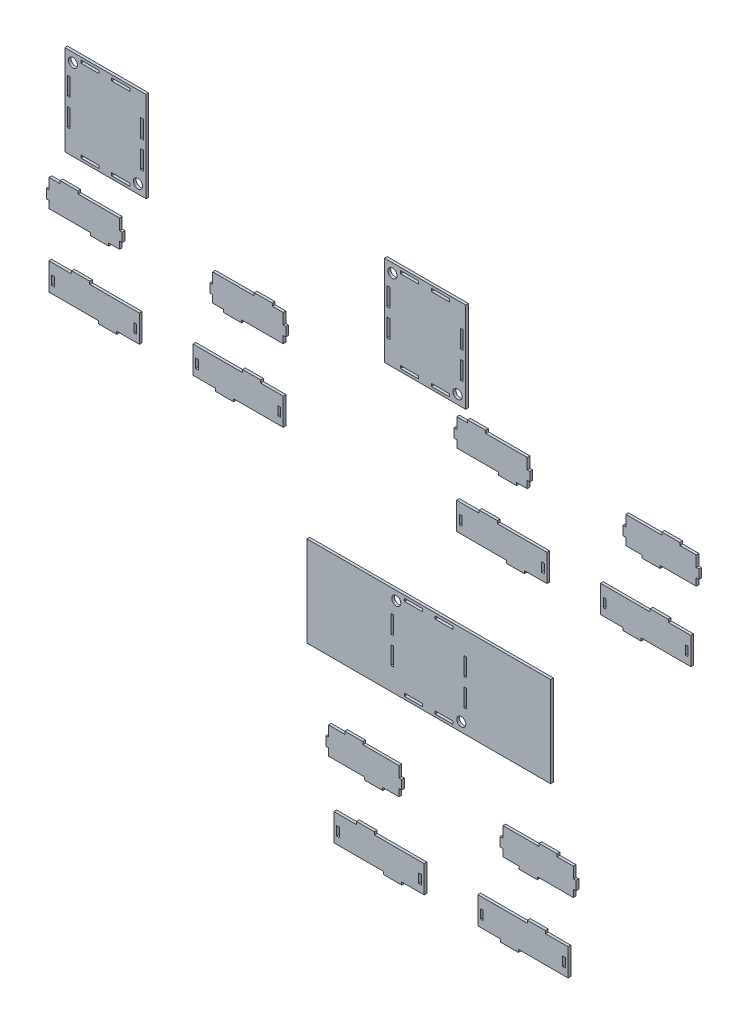
SolidWorks part; units mm, degrees
ref_plane "Спереди" through (0, 0, 0) normal (0, 0, 1) x (1, 0, 0)
ref_plane "Сверху" through (0, 0, 0) normal (0, 1, 0) x (1, 0, 0)
ref_plane "Справа" through (0, 0, 0) normal (1, 0, 0) x (0, 0, -1)
sketch "Эскиз1" plane through (0, 0, 0) normal (0, 0, 1) x (1, 0, 0)
  line L11 (-251.1655, 214.705) -> (-254.1655, 214.705)
  line L32 (-251.1655, 226.705) -> (-239.1655, 226.705)
  line L42 (-196.2718, 116.5938) -> (-196.2718, 113.5938)
  line L43 (-251.2718, 146.5938) -> (-226.2718, 146.5938)
  line L44 (-251.2718, 146.5938) -> (-251.2718, 116.5938)
  line L45 (-251.2718, 116.5938) -> (-196.2718, 116.5938)
  line L46 (-151.2718, 146.5938) -> (-151.2718, 116.5938)
  line L47 (-248.2718, 134.5938) -> (-245.2718, 134.5938)
  line L48 (-248.2718, 134.5938) -> (-248.2718, 124.5938)
  line L49 (-248.2718, 124.5938) -> (-245.2718, 124.5938)
  line L50 (-245.2718, 134.5938) -> (-245.2718, 124.5938)
  line L51 (-157.2718, 134.5938) -> (-154.2718, 134.5938)
  line L52 (-157.2718, 134.5938) -> (-157.2718, 124.5938)
  line L53 (-157.2718, 124.5938) -> (-154.2718, 124.5938)
  line L54 (-154.2718, 134.5938) -> (-154.2718, 124.5938)
  line L55 (-196.2718, 113.5938) -> (-176.2718, 113.5938)
  line L56 (-176.2718, 113.5938) -> (-176.2718, 116.5938)
  line L57 (-226.2718, 146.5938) -> (-226.2718, 149.5938)
  line L58 (-226.2718, 149.5938) -> (-206.2718, 149.5938)
  line L59 (-206.2718, 149.5938) -> (-206.2718, 146.5938)
  line L60 (-176.2718, 116.5938) -> (-151.2718, 116.5938)
  line L61 (-206.2718, 146.5938) -> (-151.2718, 146.5938)
  line L93 (-121.597, -804.4399) -> (-121.597, 49195.5601) construction
  line L114 (-58.0285, 196.705) -> (-70.0285, 196.705)
  line L175 (-70.0285, 204.705) -> (-70.0285, 196.705)
  line L196 (-24.0285, 226.705) -> (-70.0285, 226.705)
  line L247 (-233.8227, 359.8799) -> (-143.8227, 359.8799)
  line L248 (-233.8227, 359.8799) -> (-233.8227, 259.8799)
  line L249 (-233.8227, 259.8799) -> (-143.8227, 259.8799)
  line L250 (-143.8227, 359.8799) -> (-143.8227, 259.8799)
  line L251 (-230.8227, 304.8799) -> (-227.8227, 304.8799)
  line L252 (-230.8227, 304.8799) -> (-230.8227, 284.8799)
  line L253 (-230.8227, 284.8799) -> (-227.8227, 284.8799)
  line L254 (-227.8227, 304.8799) -> (-227.8227, 284.8799)
  line L255 (-215.8227, 356.8799) -> (-195.8227, 356.8799)
  line L256 (-215.8227, 356.8799) -> (-215.8227, 353.8799)
  line L257 (-215.8227, 353.8799) -> (-195.8227, 353.8799)
  line L258 (-195.8227, 356.8799) -> (-195.8227, 353.8799)
  line L259 (-146.8227, 304.8799) -> (-149.8227, 304.8799)
  line L260 (-146.8227, 304.8799) -> (-146.8227, 284.8799)
  line L261 (-146.8227, 284.8799) -> (-149.8227, 284.8799)
  line L262 (-149.8227, 304.8799) -> (-149.8227, 284.8799)
  line L263 (-215.8227, 262.8799) -> (-195.8227, 262.8799)
  line L264 (-215.8227, 262.8799) -> (-215.8227, 265.8799)
  line L265 (-215.8227, 265.8799) -> (-195.8227, 265.8799)
  line L266 (-195.8227, 262.8799) -> (-195.8227, 265.8799)
  line L267 (-181.8227, 353.8799) -> (-161.8227, 353.8799)
  line L268 (-181.8227, 353.8799) -> (-181.8227, 356.8799)
  line L269 (-181.8227, 356.8799) -> (-161.8227, 356.8799)
  line L270 (-161.8227, 353.8799) -> (-161.8227, 356.8799)
  line L271 (-146.8227, 334.8799) -> (-149.8227, 334.8799)
  line L272 (-146.8227, 334.8799) -> (-146.8227, 314.8799)
  line L273 (-146.8227, 314.8799) -> (-149.8227, 314.8799)
  line L274 (-149.8227, 334.8799) -> (-149.8227, 314.8799)
  line L275 (-230.8227, 334.8799) -> (-227.8227, 334.8799)
  line L276 (-230.8227, 334.8799) -> (-230.8227, 314.8799)
  line L277 (-230.8227, 314.8799) -> (-227.8227, 314.8799)
  line L278 (-227.8227, 334.8799) -> (-227.8227, 314.8799)
  line L279 (-181.8227, 265.8799) -> (-161.8227, 265.8799)
  line L280 (-181.8227, 265.8799) -> (-181.8227, 262.8799)
  line L281 (-181.8227, 262.8799) -> (-161.8227, 262.8799)
  line L282 (-161.8227, 265.8799) -> (-161.8227, 262.8799)
  line L318 (-251.1655, 226.705) -> (-251.1655, 214.705)
  line L319 (-251.1655, 196.705) -> (-205.1655, 196.705)
  line L320 (-173.1655, 226.705) -> (-173.1655, 214.705)
  line L321 (-254.1655, 214.705) -> (-254.1655, 204.705)
  line L322 (-254.1655, 204.705) -> (-251.1655, 204.705)
  line L323 (-205.1655, 196.705) -> (-205.1655, 193.705)
  line L324 (-205.1655, 193.705) -> (-185.1655, 193.705)
  line L325 (-185.1655, 193.705) -> (-185.1655, 196.705)
  line L326 (-173.1655, 214.705) -> (-170.1655, 214.705)
  line L327 (-170.1655, 214.705) -> (-170.1655, 204.705)
  line L328 (-170.1655, 204.705) -> (-173.1655, 204.705)
  line L329 (-239.1655, 226.705) -> (-239.1655, 229.705)
  line L330 (-239.1655, 229.705) -> (-219.1655, 229.705)
  line L331 (-219.1655, 229.705) -> (-219.1655, 226.705)
  line L332 (-251.1655, 204.705) -> (-251.1655, 196.705)
  line L333 (-219.1655, 226.705) -> (-173.1655, 226.705)
  line L334 (-173.1655, 204.705) -> (-173.1655, 196.705)
  line L335 (-185.1655, 196.705) -> (-173.1655, 196.705)
  line L336 (7.9715, 204.705) -> (7.9715, 196.705)
  line L337 (-24.0285, 229.705) -> (-24.0285, 226.705)
  line L338 (-4.0285, 229.705) -> (-24.0285, 229.705)
  line L339 (-4.0285, 226.705) -> (-4.0285, 229.705)
  line L340 (-73.0285, 204.705) -> (-70.0285, 204.705)
  line L341 (-73.0285, 214.705) -> (-73.0285, 204.705)
  line L342 (-70.0285, 214.705) -> (-73.0285, 214.705)
  line L343 (-58.0285, 193.705) -> (-58.0285, 196.705)
  line L344 (-38.0285, 193.705) -> (-58.0285, 193.705)
  line L345 (-38.0285, 196.705) -> (-38.0285, 193.705)
  line L346 (10.9715, 204.705) -> (7.9715, 204.705)
  line L347 (10.9715, 214.705) -> (10.9715, 204.705)
  line L348 (-70.0285, 226.705) -> (-70.0285, 214.705)
  line L349 (7.9715, 196.705) -> (-38.0285, 196.705)
  line L350 (7.9715, 226.705) -> (7.9715, 214.705)
  line L351 (-36.9222, 146.5938) -> (-91.9222, 146.5938)
  line L352 (-66.9222, 116.5938) -> (-91.9222, 116.5938)
  line L353 (-36.9222, 149.5938) -> (-36.9222, 146.5938)
  line L354 (-16.9222, 149.5938) -> (-36.9222, 149.5938)
  line L355 (-16.9222, 146.5938) -> (-16.9222, 149.5938)
  line L356 (-66.9222, 113.5938) -> (-66.9222, 116.5938)
  line L357 (-46.9222, 113.5938) -> (-66.9222, 113.5938)
  line L358 (-88.9222, 134.5938) -> (-88.9222, 124.5938)
  line L359 (-85.9222, 124.5938) -> (-88.9222, 124.5938)
  line L360 (-85.9222, 134.5938) -> (-85.9222, 124.5938)
  line L361 (-85.9222, 134.5938) -> (-88.9222, 134.5938)
  line L362 (2.0778, 134.5938) -> (2.0778, 124.5938)
  line L363 (5.0778, 124.5938) -> (2.0778, 124.5938)
  line L364 (5.0778, 134.5938) -> (5.0778, 124.5938)
  line L365 (5.0778, 134.5938) -> (2.0778, 134.5938)
  line L366 (-91.9222, 146.5938) -> (-91.9222, 116.5938)
  line L367 (8.0778, 116.5938) -> (-46.9222, 116.5938)
  line L368 (8.0778, 146.5938) -> (8.0778, 116.5938)
  line L369 (8.0778, 146.5938) -> (-16.9222, 146.5938)
  line L370 (-46.9222, 116.5938) -> (-46.9222, 113.5938)
  line L371 (7.9715, 226.705) -> (-4.0285, 226.705)
  line L372 (7.9715, 214.705) -> (10.9715, 214.705)
  line L398 (120.1372, 334.937) -> (210.1372, 334.937)
  line L399 (120.1372, 334.937) -> (120.1372, 234.937)
  line L400 (120.1372, 234.937) -> (210.1372, 234.937)
  line L401 (210.1372, 334.937) -> (210.1372, 234.937)
  line L402 (123.1372, 279.937) -> (126.1372, 279.937)
  line L403 (123.1372, 279.937) -> (123.1372, 259.937)
  line L404 (123.1372, 259.937) -> (126.1372, 259.937)
  line L405 (126.1372, 279.937) -> (126.1372, 259.937)
  line L406 (138.1372, 331.937) -> (158.1372, 331.937)
  line L407 (138.1372, 331.937) -> (138.1372, 328.937)
  line L408 (138.1372, 328.937) -> (158.1372, 328.937)
  line L409 (158.1372, 331.937) -> (158.1372, 328.937)
  line L410 (207.1372, 279.937) -> (204.1372, 279.937)
  line L411 (207.1372, 279.937) -> (207.1372, 259.937)
  line L412 (207.1372, 259.937) -> (204.1372, 259.937)
  line L413 (204.1372, 279.937) -> (204.1372, 259.937)
  line L414 (138.1372, 237.937) -> (158.1372, 237.937)
  line L415 (138.1372, 237.937) -> (138.1372, 240.937)
  line L416 (138.1372, 240.937) -> (158.1372, 240.937)
  line L417 (158.1372, 237.937) -> (158.1372, 240.937)
  line L418 (172.1372, 328.937) -> (192.1372, 328.937)
  line L419 (172.1372, 328.937) -> (172.1372, 331.937)
  line L420 (172.1372, 331.937) -> (192.1372, 331.937)
  line L421 (192.1372, 328.937) -> (192.1372, 331.937)
  line L422 (207.1372, 309.937) -> (204.1372, 309.937)
  line L423 (207.1372, 309.937) -> (207.1372, 289.937)
  line L424 (207.1372, 289.937) -> (204.1372, 289.937)
  line L425 (204.1372, 309.937) -> (204.1372, 289.937)
  line L426 (123.1372, 309.937) -> (126.1372, 309.937)
  line L427 (123.1372, 309.937) -> (123.1372, 289.937)
  line L428 (123.1372, 289.937) -> (126.1372, 289.937)
  line L429 (126.1372, 309.937) -> (126.1372, 289.937)
  line L430 (172.1372, 240.937) -> (192.1372, 240.937)
  line L431 (172.1372, 240.937) -> (172.1372, 237.937)
  line L432 (172.1372, 237.937) -> (192.1372, 237.937)
  line L433 (192.1372, 240.937) -> (192.1372, 237.937)
  line L514 (124.2667, 22.8612) -> (214.2667, 22.8612)
  line L516 (124.2667, -77.1388) -> (214.2667, -77.1388)
  line L518 (127.2667, -32.1388) -> (130.2667, -32.1388)
  line L519 (127.2667, -32.1388) -> (127.2667, -52.1388)
  line L520 (127.2667, -52.1388) -> (130.2667, -52.1388)
  line L521 (130.2667, -32.1388) -> (130.2667, -52.1388)
  line L522 (142.2667, 19.8612) -> (162.2667, 19.8612)
  line L523 (142.2667, 19.8612) -> (142.2667, 16.8612)
  line L524 (142.2667, 16.8612) -> (162.2667, 16.8612)
  line L525 (162.2667, 19.8612) -> (162.2667, 16.8612)
  line L526 (211.2667, -32.1388) -> (208.2667, -32.1388)
  line L527 (211.2667, -32.1388) -> (211.2667, -52.1388)
  line L528 (211.2667, -52.1388) -> (208.2667, -52.1388)
  line L529 (208.2667, -32.1388) -> (208.2667, -52.1388)
  line L530 (142.2667, -74.1388) -> (162.2667, -74.1388)
  line L531 (142.2667, -74.1388) -> (142.2667, -71.1388)
  line L532 (142.2667, -71.1388) -> (162.2667, -71.1388)
  line L533 (162.2667, -74.1388) -> (162.2667, -71.1388)
  line L534 (176.2667, 16.8612) -> (196.2667, 16.8612)
  line L535 (176.2667, 16.8612) -> (176.2667, 19.8612)
  line L536 (176.2667, 19.8612) -> (196.2667, 19.8612)
  line L537 (196.2667, 16.8612) -> (196.2667, 19.8612)
  line L538 (211.2667, -2.1388) -> (208.2667, -2.1388)
  line L539 (211.2667, -2.1388) -> (211.2667, -22.1388)
  line L540 (211.2667, -22.1388) -> (208.2667, -22.1388)
  line L541 (208.2667, -2.1388) -> (208.2667, -22.1388)
  line L542 (127.2667, -2.1388) -> (130.2667, -2.1388)
  line L543 (127.2667, -2.1388) -> (127.2667, -22.1388)
  line L544 (127.2667, -22.1388) -> (130.2667, -22.1388)
  line L545 (130.2667, -2.1388) -> (130.2667, -22.1388)
  line L546 (176.2667, -71.1388) -> (196.2667, -71.1388)
  line L547 (176.2667, -71.1388) -> (176.2667, -74.1388)
  line L548 (176.2667, -74.1388) -> (196.2667, -74.1388)
  line L549 (196.2667, -71.1388) -> (196.2667, -74.1388)
  line L605 (124.2667, 22.8612) -> (34.2667, 22.8612)
  line L610 (34.2667, 22.8612) -> (34.2667, -77.1388)
  line L611 (34.2667, -77.1388) -> (124.2667, -77.1388)
  line L612 (214.2667, -77.1388) -> (304.2667, -77.1388)
  line L613 (304.2667, -77.1388) -> (304.2667, 22.8612)
  line L614 (304.2667, 22.8612) -> (214.2667, 22.8612)
  line L615 (200.25, 210.8868) -> (197.25, 210.8868)
  line L616 (200.25, 222.8868) -> (212.25, 222.8868)
  line L617 (255.1437, 112.7755) -> (255.1437, 109.7755)
  line L618 (200.1437, 142.7755) -> (225.1437, 142.7755)
  line L619 (200.1437, 142.7755) -> (200.1437, 112.7755)
  line L620 (200.1437, 112.7755) -> (255.1437, 112.7755)
  line L621 (300.1437, 142.7755) -> (300.1437, 112.7755)
  line L622 (203.1437, 130.7755) -> (206.1437, 130.7755)
  line L623 (203.1437, 130.7755) -> (203.1437, 120.7755)
  line L624 (203.1437, 120.7755) -> (206.1437, 120.7755)
  line L625 (206.1437, 130.7755) -> (206.1437, 120.7755)
  line L626 (294.1437, 130.7755) -> (297.1437, 130.7755)
  line L627 (294.1437, 130.7755) -> (294.1437, 120.7755)
  line L628 (294.1437, 120.7755) -> (297.1437, 120.7755)
  line L629 (297.1437, 130.7755) -> (297.1437, 120.7755)
  line L630 (255.1437, 109.7755) -> (275.1437, 109.7755)
  line L631 (275.1437, 109.7755) -> (275.1437, 112.7755)
  line L632 (225.1437, 142.7755) -> (225.1437, 145.7755)
  line L633 (225.1437, 145.7755) -> (245.1437, 145.7755)
  line L634 (245.1437, 145.7755) -> (245.1437, 142.7755)
  line L635 (275.1437, 112.7755) -> (300.1437, 112.7755)
  line L636 (245.1437, 142.7755) -> (300.1437, 142.7755)
  line L637 (405.387, 192.8868) -> (387.387, 192.8868)
  line L638 (387.387, 200.8868) -> (387.387, 192.8868)
  line L639 (427.387, 222.8868) -> (387.387, 222.8868)
  line L640 (200.25, 222.8868) -> (200.25, 210.8868)
  line L641 (200.25, 192.8868) -> (246.25, 192.8868)
  line L642 (278.25, 222.8868) -> (278.25, 210.8868)
  line L643 (197.25, 210.8868) -> (197.25, 200.8868)
  line L644 (197.25, 200.8868) -> (200.25, 200.8868)
  line L645 (246.25, 192.8868) -> (246.25, 189.8868)
  line L646 (246.25, 189.8868) -> (266.25, 189.8868)
  line L647 (266.25, 189.8868) -> (266.25, 192.8868)
  line L648 (278.25, 210.8868) -> (281.25, 210.8868)
  line L649 (281.25, 210.8868) -> (281.25, 200.8868)
  line L650 (281.25, 200.8868) -> (278.25, 200.8868)
  line L651 (212.25, 222.8868) -> (212.25, 225.8868)
  line L652 (212.25, 225.8868) -> (232.25, 225.8868)
  line L653 (232.25, 225.8868) -> (232.25, 222.8868)
  line L654 (200.25, 200.8868) -> (200.25, 192.8868)
  line L655 (232.25, 222.8868) -> (278.25, 222.8868)
  line L656 (278.25, 200.8868) -> (278.25, 192.8868)
  line L657 (266.25, 192.8868) -> (278.25, 192.8868)
  line L658 (465.387, 200.8868) -> (465.387, 192.8868)
  line L659 (427.387, 225.8868) -> (427.387, 222.8868)
  line L660 (447.387, 225.8868) -> (427.387, 225.8868)
  line L661 (447.387, 222.8868) -> (447.387, 225.8868)
  line L662 (384.387, 200.8868) -> (387.387, 200.8868)
  line L663 (384.387, 210.8868) -> (384.387, 200.8868)
  line L664 (387.387, 210.8868) -> (384.387, 210.8868)
  line L665 (405.387, 189.8868) -> (405.387, 192.8868)
  line L666 (425.387, 189.8868) -> (405.387, 189.8868)
  line L667 (425.387, 192.8868) -> (425.387, 189.8868)
  line L668 (468.387, 200.8868) -> (465.387, 200.8868)
  line L669 (468.387, 210.8868) -> (468.387, 200.8868)
  line L670 (387.387, 222.8868) -> (387.387, 210.8868)
  line L671 (465.387, 192.8868) -> (425.387, 192.8868)
  line L672 (465.387, 222.8868) -> (465.387, 210.8868)
  line L673 (414.4934, 142.7755) -> (359.4934, 142.7755)
  line L674 (384.4934, 112.7755) -> (359.4934, 112.7755)
  line L675 (414.4934, 145.7755) -> (414.4934, 142.7755)
  line L676 (434.4934, 145.7755) -> (414.4934, 145.7755)
  line L677 (434.4934, 142.7755) -> (434.4934, 145.7755)
  line L678 (384.4934, 109.7755) -> (384.4934, 112.7755)
  line L679 (404.4934, 109.7755) -> (384.4934, 109.7755)
  line L680 (362.4934, 130.7755) -> (362.4934, 120.7755)
  line L681 (365.4934, 120.7755) -> (362.4934, 120.7755)
  line L682 (365.4934, 130.7755) -> (365.4934, 120.7755)
  line L683 (365.4934, 130.7755) -> (362.4934, 130.7755)
  line L684 (453.4934, 130.7755) -> (453.4934, 120.7755)
  line L685 (456.4934, 120.7755) -> (453.4934, 120.7755)
  line L686 (456.4934, 130.7755) -> (456.4934, 120.7755)
  line L687 (456.4934, 130.7755) -> (453.4934, 130.7755)
  line L688 (359.4934, 142.7755) -> (359.4934, 112.7755)
  line L689 (459.4934, 112.7755) -> (404.4934, 112.7755)
  line L690 (459.4934, 142.7755) -> (459.4934, 112.7755)
  line L691 (459.4934, 142.7755) -> (434.4934, 142.7755)
  line L692 (404.4934, 112.7755) -> (404.4934, 109.7755)
  line L693 (465.387, 222.8868) -> (447.387, 222.8868)
  line L694 (465.387, 210.8868) -> (468.387, 210.8868)
  line L695 (58.2619, -155.6255) -> (55.2619, -155.6255)
  line L696 (58.2619, -143.6255) -> (76.2619, -143.6255)
  line L697 (119.1556, -253.7368) -> (119.1556, -256.7368)
  line L698 (64.1556, -223.7368) -> (89.1556, -223.7368)
  line L699 (64.1556, -223.7368) -> (64.1556, -253.7368)
  line L700 (64.1556, -253.7368) -> (119.1556, -253.7368)
  line L701 (164.1556, -223.7368) -> (164.1556, -253.7368)
  line L702 (67.1556, -235.7368) -> (70.1556, -235.7368)
  line L703 (67.1556, -235.7368) -> (67.1556, -245.7368)
  line L704 (67.1556, -245.7368) -> (70.1556, -245.7368)
  line L705 (70.1556, -235.7368) -> (70.1556, -245.7368)
  line L706 (158.1556, -235.7368) -> (161.1556, -235.7368)
  line L707 (158.1556, -235.7368) -> (158.1556, -245.7368)
  line L708 (158.1556, -245.7368) -> (161.1556, -245.7368)
  line L709 (161.1556, -235.7368) -> (161.1556, -245.7368)
  line L710 (119.1556, -256.7368) -> (139.1556, -256.7368)
  line L711 (139.1556, -256.7368) -> (139.1556, -253.7368)
  line L712 (89.1556, -223.7368) -> (89.1556, -220.7368)
  line L713 (89.1556, -220.7368) -> (109.1556, -220.7368)
  line L714 (109.1556, -220.7368) -> (109.1556, -223.7368)
  line L715 (139.1556, -253.7368) -> (164.1556, -253.7368)
  line L716 (109.1556, -223.7368) -> (164.1556, -223.7368)
  line L717 (269.3989, -173.6255) -> (251.3989, -173.6255)
  line L718 (251.3989, -165.6255) -> (251.3989, -173.6255)
  line L719 (291.3989, -143.6255) -> (251.3989, -143.6255)
  line L720 (58.2619, -143.6255) -> (58.2619, -155.6255)
  line L721 (58.2619, -173.6255) -> (98.2619, -173.6255)
  line L722 (136.2619, -143.6255) -> (136.2619, -155.6255)
  line L723 (55.2619, -155.6255) -> (55.2619, -165.6255)
  line L724 (55.2619, -165.6255) -> (58.2619, -165.6255)
  line L725 (98.2619, -173.6255) -> (98.2619, -176.6255)
  line L726 (98.2619, -176.6255) -> (118.2619, -176.6255)
  line L727 (118.2619, -176.6255) -> (118.2619, -173.6255)
  line L728 (136.2619, -155.6255) -> (139.2619, -155.6255)
  line L729 (139.2619, -155.6255) -> (139.2619, -165.6255)
  line L730 (139.2619, -165.6255) -> (136.2619, -165.6255)
  line L731 (76.2619, -143.6255) -> (76.2619, -140.6255)
  line L732 (76.2619, -140.6255) -> (96.2619, -140.6255)
  line L733 (96.2619, -140.6255) -> (96.2619, -143.6255)
  line L734 (58.2619, -165.6255) -> (58.2619, -173.6255)
  line L735 (96.2619, -143.6255) -> (136.2619, -143.6255)
  line L736 (136.2619, -165.6255) -> (136.2619, -173.6255)
  line L737 (118.2619, -173.6255) -> (136.2619, -173.6255)
  line L738 (329.3989, -165.6255) -> (329.3989, -173.6255)
  line L739 (291.3989, -140.6255) -> (291.3989, -143.6255)
  line L740 (311.3989, -140.6255) -> (291.3989, -140.6255)
  line L741 (311.3989, -143.6255) -> (311.3989, -140.6255)
  line L742 (248.3989, -165.6255) -> (251.3989, -165.6255)
  line L743 (248.3989, -155.6255) -> (248.3989, -165.6255)
  line L744 (251.3989, -155.6255) -> (248.3989, -155.6255)
  line L745 (269.3989, -176.6255) -> (269.3989, -173.6255)
  line L746 (289.3989, -176.6255) -> (269.3989, -176.6255)
  line L747 (289.3989, -173.6255) -> (289.3989, -176.6255)
  line L748 (332.3989, -165.6255) -> (329.3989, -165.6255)
  line L749 (332.3989, -155.6255) -> (332.3989, -165.6255)
  line L750 (251.3989, -143.6255) -> (251.3989, -155.6255)
  line L751 (329.3989, -173.6255) -> (289.3989, -173.6255)
  line L752 (329.3989, -143.6255) -> (329.3989, -155.6255)
  line L753 (278.5052, -223.7368) -> (223.5052, -223.7368)
  line L754 (248.5052, -253.7368) -> (223.5052, -253.7368)
  line L755 (278.5052, -220.7368) -> (278.5052, -223.7368)
  line L756 (298.5052, -220.7368) -> (278.5052, -220.7368)
  line L757 (298.5052, -223.7368) -> (298.5052, -220.7368)
  line L758 (248.5052, -256.7368) -> (248.5052, -253.7368)
  line L759 (268.5052, -256.7368) -> (248.5052, -256.7368)
  line L760 (226.5052, -235.7368) -> (226.5052, -245.7368)
  line L761 (229.5052, -245.7368) -> (226.5052, -245.7368)
  line L762 (229.5052, -235.7368) -> (229.5052, -245.7368)
  line L763 (229.5052, -235.7368) -> (226.5052, -235.7368)
  line L764 (317.5052, -235.7368) -> (317.5052, -245.7368)
  line L765 (320.5052, -245.7368) -> (317.5052, -245.7368)
  line L766 (320.5052, -235.7368) -> (320.5052, -245.7368)
  line L767 (320.5052, -235.7368) -> (317.5052, -235.7368)
  line L768 (223.5052, -223.7368) -> (223.5052, -253.7368)
  line L769 (323.5052, -253.7368) -> (268.5052, -253.7368)
  line L770 (323.5052, -223.7368) -> (323.5052, -253.7368)
  line L771 (323.5052, -223.7368) -> (298.5052, -223.7368)
  line L772 (268.5052, -253.7368) -> (268.5052, -256.7368)
  line L773 (329.3989, -143.6255) -> (311.3989, -143.6255)
  line L774 (329.3989, -155.6255) -> (332.3989, -155.6255)
  circle A1 centre (-152.8227, 269.8799) radius 5
  circle A2 centre (-224.8227, 349.8799) radius 5
  circle A6 centre (201.1372, 244.937) radius 5
  circle A7 centre (129.1372, 324.937) radius 5
  circle A8 centre (205.2667, -67.1388) radius 5
  circle A9 centre (133.2667, 12.8612) radius 5
  dimension "D164" = 10
  dimension "D165" = 10
  dimension "D75" = 10
  dimension "D76" = 10
  dimension "D177" = 10
  dimension "D178" = 10
  dimension "D5" = 8
  dimension "D6" = 3
  dimension "D7" = 3
  dimension "D8" = 8
  dimension "D9" = 8
  dimension "D10" = 20
  dimension "D11" = 3
  dimension "D12" = 20
  dimension "D20" = 100
  dimension "D21" = 8
  dimension "D22" = 3
  dimension "D23" = 3
  dimension "D24" = 10
  dimension "D25" = 10
  dimension "D26" = 3
  dimension "D27" = 3
  dimension "D28" = 3
  dimension "D29" = 20
  dimension "D30" = 25
  dimension "D31" = 25
  dimension "D32" = 78
  dimension "D33" = 3
  dimension "D34" = 30
  dimension "D35" = 3
  dimension "D36" = 10
  dimension "D37" = 10
  dimension "D38" = 3
  dimension "D39" = 3
  dimension "D40" = 20
  dimension "D41" = 25
  dimension "D42" = 3
  dimension "D43" = 30
  dimension "D44" = 3
  dimension "D45" = 78
  dimension "D46" = 30
  dimension "D47" = 90
  dimension "D48" = 3
  dimension "D49" = 12
  dimension "D50" = 25
  dimension "D51" = 25
  dimension "D52" = 20
  dimension "D53" = 100
  dimension "D54" = 25
  dimension "D55" = 3
  dimension "D56" = 10
  dimension "D57" = 20
  dimension "D58" = 20
  dimension "D59" = 3
  dimension "D60" = 3
  dimension "D61" = 20
  dimension "D62" = 3
  dimension "D63" = 3
  dimension "D64" = 3
  dimension "D65" = 20
  dimension "D66" = 3
  dimension "D67" = 20
  dimension "D68" = 20
  dimension "D69" = 20
  dimension "D70" = 3
  dimension "D71" = 3
  dimension "D72" = 3
  dimension "D73" = 9
  dimension "D74" = 10
  dimension "D77" = 9
  dimension "D78" = 10
  dimension "D79" = 20
  dimension "D80" = 3
  dimension "D81" = 3
  dimension "D82" = 18
  dimension "D83" = 3
  dimension "D84" = 18
  dimension "D85" = 10
  dimension "D86" = 18
  dimension "D87" = 3
  dimension "D88" = 25
  dimension "D89" = 3
  dimension "D90" = 8
  dimension "D91" = 3
  dimension "D92" = 3
  dimension "D93" = 8
  dimension "D94" = 20
  dimension "D95" = 3
  dimension "D96" = 20
  dimension "D97" = 3
  dimension "D98" = 12
  dimension "D99" = 20
  dimension "D100" = 12
  dimension "D101" = 25
  dimension "D102" = 8
  dimension "D103" = 3
  dimension "D104" = 25
  dimension "D105" = 25
  dimension "D106" = 10
  dimension "D107" = 10
  dimension "D108" = 3
  dimension "D109" = 3
  dimension "D110" = 20
  dimension "D111" = 25
  dimension "D112" = 3
  dimension "D113" = 30
  dimension "D114" = 3
  dimension "D115" = 78
  dimension "D116" = 30
  dimension "D117" = 10
  dimension "D118" = 10
  dimension "D119" = 8
  dimension "D120" = 3
  dimension "D121" = 12
  dimension "D122" = 100
  dimension "D123" = 25
  dimension "D124" = 3
  dimension "D125" = 3
  dimension "D126" = 20
  dimension "D127" = 20
  dimension "D128" = 3
  dimension "D129" = 8
  dimension "D130" = 20
  dimension "D131" = 3
  dimension "D132" = 3
  dimension "D133" = 3
  dimension "D134" = 20
  dimension "D135" = 20
  dimension "D136" = 90
  dimension "D137" = 100
  dimension "D138" = 25
  dimension "D139" = 3
  dimension "D140" = 18
  dimension "D141" = 20
  dimension "D142" = 20
  dimension "D143" = 3
  dimension "D144" = 3
  dimension "D145" = 20
  dimension "D146" = 20
  dimension "D147" = 3
  dimension "D148" = 18
  dimension "D149" = 3
  dimension "D150" = 3
  dimension "D151" = 20
  dimension "D152" = 3
  dimension "D153" = 20
  dimension "D154" = 20
  dimension "D155" = 20
  dimension "D156" = 3
  dimension "D157" = 3
  dimension "D158" = 3
  dimension "D159" = 3
  dimension "D160" = 3
  dimension "D161" = 18
  dimension "D162" = 9
  dimension "D163" = 10
  dimension "D166" = 9
  dimension "D167" = 10
  dimension "D168" = 20
  dimension "D169" = 20
  dimension "D170" = 3
  dimension "D171" = 20
  dimension "D172" = 3
  dimension "D173" = 3
  dimension "D174" = 3
  dimension "D175" = 3
  dimension "D176" = 10
  dimension "D179" = 20
  dimension "D180" = 10
  dimension "D181" = 20
  dimension "D182" = 3
  dimension "D183" = 3
  dimension "D184" = 3
  dimension "D185" = 3
  dimension "D186" = 18
  dimension "D187" = 20
  dimension "D188" = 18
  dimension "D189" = 3
  dimension "D190" = 25
  dimension "D191" = 25
  dimension "D203" = 3
  dimension "D204" = 18
  dimension "D205" = 3
  dimension "D206" = 25
  dimension "D207" = 3
  dimension "D208" = 30
  dimension "D209" = 10
  dimension "D210" = 10
  dimension "D214" = 25
  dimension "D215" = 25
  dimension "D217" = 90
  dimension "D218" = 90
extrude "Бобышка-Вытянуть1" add sketch "Эскиз1" along normal blind 3
